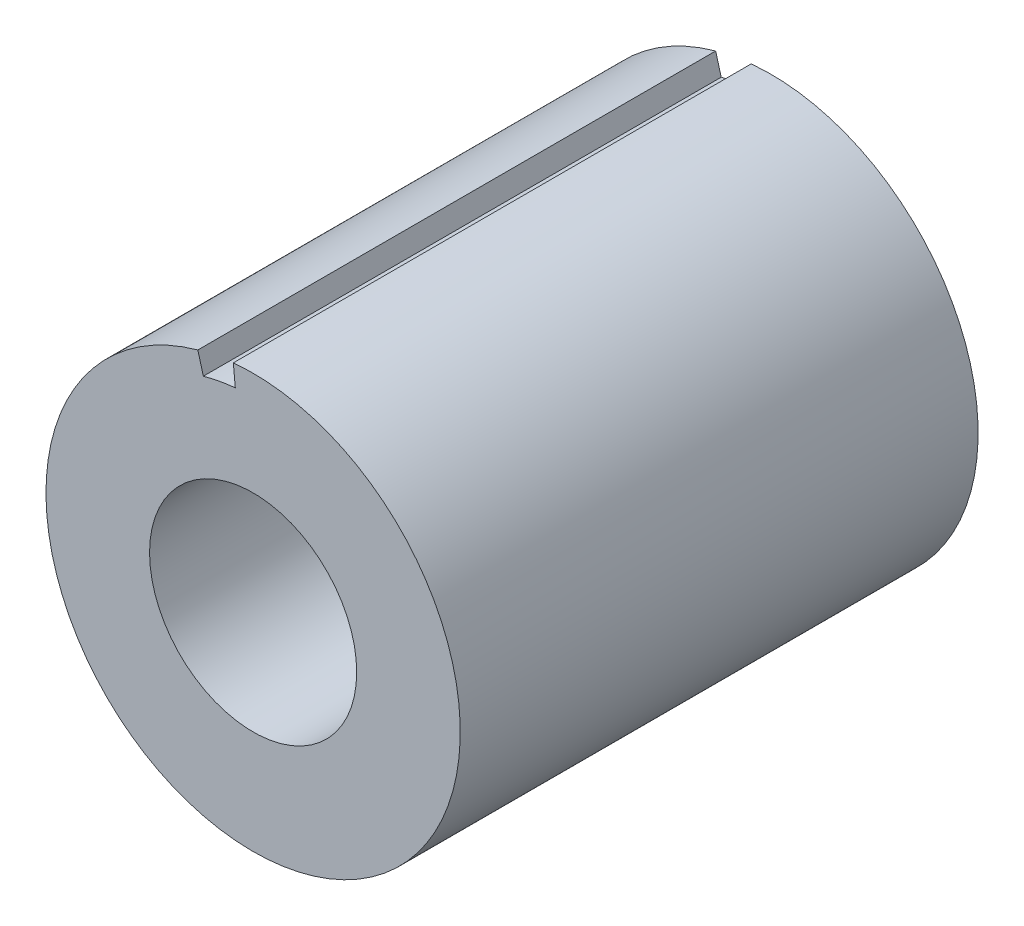
SolidWorks part; units mm, degrees
ref_plane "Front Plane" through (0, 0, 0) normal (0, 0, 1) x (1, 0, 0)
ref_plane "Top Plane" through (0, 0, 0) normal (0, 1, 0) x (1, 0, 0)
ref_plane "Right Plane" through (0, 0, 0) normal (1, 0, 0) x (0, 0, -1)
sketch "Sketch1" plane through (0, 0, 0) normal (0, 0, 1) x (1, 0, 0)
  circle A0 centre (0, 0) radius 2
  circle A1 centre (0, 0) radius 4
  dimension "D1" = 4
  dimension "D2" = 8
extrude "Boss-Extrude1" add sketch "Sketch1" along normal blind 10
sketch "Sketch2" plane through (0, 0, 10) normal (0, 0, 1) x (1, 0, 0)
  line L0 (-0.9611, 3.4693) -> (-1.4316, 5.1676)
  line L2 (-0.5125, 5.3377) -> (-0.344, 3.5835)
  circle A0 centre (0, 0) radius 4 construction
  arc A1 (-0.344, 3.5835) -> (-0.9611, 3.4693) centre (0, 0) ccw
  arc A2 (-0.5125, 5.3377) -> (-1.4316, 5.1676) centre (0, 0) ccw
  dimension "D1" = 0.4
  dimension "D2" = 10
extrude "Cut-Extrude1" cut sketch "Sketch2" against normal blind 11
